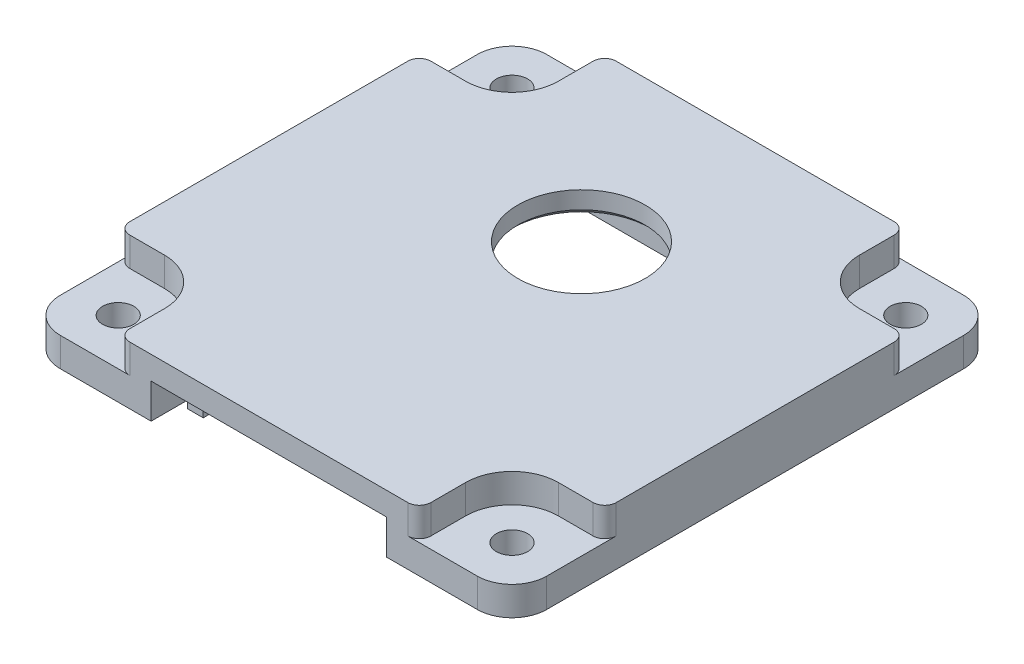
SolidWorks part; units mm, degrees
material "ABS"
ref_plane "Front Plane" through (0, 0, 0) normal (0, 0, 1) x (1, 0, 0)
ref_plane "Top Plane" through (0, 0, 0) normal (0, 1, 0) x (1, 0, 0)
ref_plane "Right Plane" through (0, 0, 0) normal (1, 0, 0) x (0, 0, -1)
sketch "Sketch2" plane through (0, 0, 0) normal (0, 1, 0) x (1, 0, 0)
  line L0 (0, 0) -> (0, 6) construction
  line L1 (-21, 21) -> (21, 21)
  line L2 (-21, 21) -> (-21, -21)
  line L3 (-21, -21) -> (21, -21)
  line L4 (21, 21) -> (21, -21)
  line L5 (-21, 21) -> (21, -21) construction
  line L6 (-21, -21) -> (21, 21) construction
  circle A0 centre (0, 6) radius 5.5
  point P0 (0, 0)
  dimension "D3" = 11
  dimension "D1" = 42
  dimension "D2" = 42
  dimension "D4" = 6
extrude "Boss-Extrude1" add sketch "Sketch2" against normal blind 2
ref_plane "Plane1" through (0, 0, -6) normal (0, 0, 1) x (1, 0, 0)
sketch "Sketch3" plane through (0, 0, -6) normal (0, 0, 1) x (1, 0, 0)
  line L1 (-5.5, 0) -> (-6.25, 0)
  line L2 (-6.25, 0) -> (-6.25, 3)
  line L4 (-6.25, 3) -> (-5.25, 3)
  line L8 (-5.5, 2) -> (-5.5, 0)
  line L9 (0, 0) -> (0, 7.3617) construction
  line L10 (-5.5, 2) -> (-4.5, 2.727)
  line L11 (-4.5, 2.727) -> (-5.25, 3)
  line L13 (0, 1.0892) -> (-5.25, 3) construction
  dimension "D1" = 70
  dimension "D2" = 3
  dimension "D3" = 1
  dimension "D4" = 0.75
  dimension "D5" = 0.75
  dimension "D6" = 2
revolve "Revolve1" [suppressed] add sketch "Sketch3" angle 360 about L9
sketch "Sketch4" plane through (0, -2, 0) normal (0, -1, 0) x (1, 0, 0)
  line L8 (-21, 21) -> (21, 21)
  line L9 (-21, 21) -> (-21, -21)
  line L10 (-21, -21) -> (21, -21)
  line L11 (21, 21) -> (21, -21)
  line L12 (-21, 21) -> (21, -21) construction
  line L13 (-21, -21) -> (21, 21) construction
  line L14 (-17, 11.5228) -> (-17, -11.5228)
  line L15 (-11.5228, -17) -> (11.5228, -17)
  line L16 (17, 11.5228) -> (17, -11.5228)
  line L17 (-11.5228, 17) -> (11.5228, 17)
  arc A12 (-16.5455, -12.0207) -> (-12.0207, -16.5455) centre (-17, -17) cw
  arc A13 (12.0207, -16.5455) -> (16.5455, -12.0207) centre (17, -17) cw
  arc A14 (16.5455, 12.0207) -> (12.0207, 16.5455) centre (17, 17) cw
  arc A15 (-12.0207, 16.5455) -> (-16.5455, 12.0207) centre (-17, 17) cw
  arc A16 (-16.5455, -12.0207) -> (-17, -11.5228) centre (-16.5, -11.5228) cw
  arc A17 (-12.0207, -16.5455) -> (-11.5228, -17) centre (-11.5228, -16.5) ccw
  arc A18 (12.0207, -16.5455) -> (11.5228, -17) centre (11.5228, -16.5) cw
  arc A19 (16.5455, -12.0207) -> (17, -11.5228) centre (16.5, -11.5228) ccw
  arc A20 (16.5455, 12.0207) -> (17, 11.5228) centre (16.5, 11.5228) cw
  arc A21 (12.0207, 16.5455) -> (11.5228, 17) centre (11.5228, 16.5) ccw
  arc A22 (-12.0207, 16.5455) -> (-11.5228, 17) centre (-11.5228, 16.5) cw
  arc A23 (-16.5455, 12.0207) -> (-17, 11.5228) centre (-16.5, 11.5228) ccw
  point P32 (0, 0)
extrude "Boss-Extrude2" add sketch "Sketch4" along normal blind 3
sketch "Sketch6" plane through (0, -2, 0) normal (0, -1, 0) x (1, 0, 0)
  line L8 (-16.5, 11.5228) -> (-16.5, -11.5228)
  line L9 (-11.5228, -16.5) -> (11.5228, -16.5)
  line L10 (16.5, -11.5228) -> (16.5, 11.5228)
  line L11 (11.5228, 16.5) -> (-11.5228, 16.5)
  line L12 (-16.5, 11.5228) -> (-16.5, -11.5228)
  line L13 (-11.5228, -16.5) -> (11.5228, -16.5)
  line L14 (16.5, -11.5228) -> (16.5, 11.5228)
  line L15 (11.5228, 16.5) -> (-11.5228, 16.5)
  line L16 (-17, 11.5228) -> (-17, -11.5228)
  line L17 (-11.5228, -17) -> (11.5228, -17)
  line L18 (17, -11.5228) -> (17, 11.5228)
  line L19 (11.5228, 17) -> (-11.5228, 17)
  line L20 (-17, 11.5228) -> (-17, -11.5228)
  line L21 (-11.5228, -17) -> (11.5228, -17)
  line L22 (17, -11.5228) -> (17, 11.5228)
  line L23 (11.5228, 17) -> (-11.5228, 17)
  arc A24 (-11.5228, -16.5) -> (-16.5, -11.5228) centre (-17, -17) ccw
  arc A25 (16.5, -11.5228) -> (11.5228, -16.5) centre (17, -17) ccw
  arc A26 (11.5228, 16.5) -> (16.5, 11.5228) centre (17, 17) ccw
  arc A27 (-16.5, 11.5228) -> (-11.5228, 16.5) centre (-17, 17) ccw
  arc A28 (-11.5228, -16.5) -> (-16.5, -11.5228) centre (-17, -17) ccw
  arc A29 (16.5, -11.5228) -> (11.5228, -16.5) centre (17, -17) ccw
  arc A30 (11.5228, 16.5) -> (16.5, 11.5228) centre (17, 17) ccw
  arc A31 (-16.5, 11.5228) -> (-11.5228, 16.5) centre (-17, 17) ccw
  arc A32 (-17, -11.5228) -> (-16.5455, -12.0207) centre (-16.5, -11.5228) ccw
  arc A33 (-12.0207, -16.5455) -> (-16.5455, -12.0207) centre (-17, -17) ccw
  arc A34 (-12.0207, -16.5455) -> (-11.5228, -17) centre (-11.5228, -16.5) ccw
  arc A35 (11.5228, -17) -> (12.0207, -16.5455) centre (11.5228, -16.5) ccw
  arc A36 (16.5455, -12.0207) -> (12.0207, -16.5455) centre (17, -17) ccw
  arc A37 (16.5455, -12.0207) -> (17, -11.5228) centre (16.5, -11.5228) ccw
  arc A38 (17, 11.5228) -> (16.5455, 12.0207) centre (16.5, 11.5228) ccw
  arc A39 (12.0207, 16.5455) -> (16.5455, 12.0207) centre (17, 17) ccw
  arc A40 (12.0207, 16.5455) -> (11.5228, 17) centre (11.5228, 16.5) ccw
  arc A41 (-11.5228, 17) -> (-12.0207, 16.5455) centre (-11.5228, 16.5) ccw
  arc A42 (-16.5455, 12.0207) -> (-12.0207, 16.5455) centre (-17, 17) ccw
  arc A43 (-16.5455, 12.0207) -> (-17, 11.5228) centre (-16.5, 11.5228) ccw
  arc A44 (-17, -11.5228) -> (-16.5455, -12.0207) centre (-16.5, -11.5228) ccw
  arc A45 (-12.0207, -16.5455) -> (-16.5455, -12.0207) centre (-17, -17) ccw
  arc A46 (-12.0207, -16.5455) -> (-11.5228, -17) centre (-11.5228, -16.5) ccw
  arc A47 (11.5228, -17) -> (12.0207, -16.5455) centre (11.5228, -16.5) ccw
  arc A48 (16.5455, -12.0207) -> (12.0207, -16.5455) centre (17, -17) ccw
  arc A49 (16.5455, -12.0207) -> (17, -11.5228) centre (16.5, -11.5228) ccw
  arc A50 (17, 11.5228) -> (16.5455, 12.0207) centre (16.5, 11.5228) ccw
  arc A51 (12.0207, 16.5455) -> (16.5455, 12.0207) centre (17, 17) ccw
  arc A52 (12.0207, 16.5455) -> (11.5228, 17) centre (11.5228, 16.5) ccw
  arc A53 (-11.5228, 17) -> (-12.0207, 16.5455) centre (-11.5228, 16.5) ccw
  arc A54 (-16.5455, 12.0207) -> (-12.0207, 16.5455) centre (-17, 17) ccw
  arc A55 (-16.5455, 12.0207) -> (-17, 11.5228) centre (-16.5, 11.5228) ccw
  dimension "D1" = 0.5
  dimension "D2" = 0
extrude "Boss-Extrude3" add sketch "Sketch6" along normal up to surface (3 mm away) up to face at (0, -5, 0)
sketch "Sketch7" plane through (0, -2, 0) normal (0, -1, 0) x (1, 0, 0)
  line L8 (10.6754, 15.5) -> (-10.6754, 15.5)
  line L9 (-15.5, 10.6754) -> (-15.5, -10.6754)
  line L10 (-10.6754, -15.5) -> (10.6754, -15.5)
  line L11 (15.5, -10.6754) -> (15.5, 10.6754)
  line L12 (10.6754, 15.5) -> (-10.6754, 15.5)
  line L13 (-15.5, 10.6754) -> (-15.5, -10.6754)
  line L14 (-10.6754, -15.5) -> (10.6754, -15.5)
  line L15 (15.5, -10.6754) -> (15.5, 10.6754)
  line L16 (11.5228, 16.5) -> (-11.5228, 16.5)
  line L17 (-16.5, 11.5228) -> (-16.5, -11.5228)
  line L18 (-11.5228, -16.5) -> (11.5228, -16.5)
  line L19 (16.5, -11.5228) -> (16.5, 11.5228)
  line L20 (11.5228, 16.5) -> (-11.5228, 16.5)
  line L21 (-16.5, 11.5228) -> (-16.5, -11.5228)
  line L22 (-11.5228, -16.5) -> (11.5228, -16.5)
  line L23 (16.5, -11.5228) -> (16.5, 11.5228)
  arc A8 (10.6754, 15.5) -> (15.5, 10.6754) centre (17, 17) ccw
  arc A9 (-15.5, 10.6754) -> (-10.6754, 15.5) centre (-17, 17) ccw
  arc A10 (-10.6754, -15.5) -> (-15.5, -10.6754) centre (-17, -17) ccw
  arc A11 (15.5, -10.6754) -> (10.6754, -15.5) centre (17, -17) ccw
  arc A12 (10.6754, 15.5) -> (15.5, 10.6754) centre (17, 17) ccw
  arc A13 (-15.5, 10.6754) -> (-10.6754, 15.5) centre (-17, 17) ccw
  arc A14 (-10.6754, -15.5) -> (-15.5, -10.6754) centre (-17, -17) ccw
  arc A15 (15.5, -10.6754) -> (10.6754, -15.5) centre (17, -17) ccw
  arc A16 (11.5228, 16.5) -> (16.5, 11.5228) centre (17, 17) ccw
  arc A17 (-16.5, 11.5228) -> (-11.5228, 16.5) centre (-17, 17) ccw
  arc A18 (-11.5228, -16.5) -> (-16.5, -11.5228) centre (-17, -17) ccw
  arc A19 (16.5, -11.5228) -> (11.5228, -16.5) centre (17, -17) ccw
  arc A20 (11.5228, 16.5) -> (16.5, 11.5228) centre (17, 17) ccw
  arc A21 (-16.5, 11.5228) -> (-11.5228, 16.5) centre (-17, 17) ccw
  arc A22 (-11.5228, -16.5) -> (-16.5, -11.5228) centre (-17, -17) ccw
  arc A23 (16.5, -11.5228) -> (11.5228, -16.5) centre (17, -17) ccw
  dimension "D1" = 1
  dimension "D2" = 0
extrude "Boss-Extrude5" add sketch "Sketch7" along normal blind 5
sketch "Sketch9" plane through (0, 0, 0) normal (0, 1, 0) x (1, 0, 0)
  circle A0 centre (-17, 17) radius 1.35
  circle A1 centre (17, 17) radius 1.35
  circle A2 centre (-17, -17) radius 1.35
  circle A3 centre (17, -17) radius 1.35
  dimension "D1" = 2.7
sketch "Sketch8" plane through (0, 0, 0) normal (0, 1, 0) x (1, 0, 0)
  line L0 (-17, 13) -> (-21, 13)
  line L1 (-21, -21) -> (-21, 21) construction
  line L2 (-21, 13) -> (-21, 21)
  line L3 (-13, 17) -> (-13, 21)
  line L4 (-21, 21) -> (21, 21) construction
  line L5 (-13, 21) -> (-21, 21)
  line L6 (13, 17) -> (13, 21)
  line L7 (13, 21) -> (21, 21)
  line L8 (21, 21) -> (21, 13)
  line L9 (17, 13) -> (21, 13)
  line L10 (21, -21) -> (21, 21) construction
  line L11 (-21, -17) -> (-21, -21)
  line L12 (-21, -21) -> (-17, -21)
  line L13 (-21, -21) -> (21, -21) construction
  line L14 (-13, -17) -> (-13, -21)
  line L15 (-13, -21) -> (-17, -21)
  line L16 (-17, -13) -> (-21, -13)
  line L17 (-21, -13) -> (-21, -17)
  line L18 (17, -13) -> (21, -13)
  line L19 (21, -13) -> (21, -21)
  line L20 (21, -21) -> (17, -21)
  line L21 (13, -17) -> (13, -21)
  line L22 (13, -21) -> (17, -21)
  arc A0 (-17, 13) -> (-13, 17) centre (-17, 17) ccw
  arc A2 (13, 17) -> (17, 13) centre (17, 17) ccw
  arc A3 (17, -13) -> (13, -17) centre (17, -17) ccw
  arc A4 (-13, -17) -> (-17, -13) centre (-17, -17) ccw
extrude "Cut-Extrude1" cut sketch "Sketch8" against normal blind 2.5
extrude "Cut-Extrude2" cut sketch "Sketch9" against normal through all
fillet "Fillet1" radius 3 4 edges at (21, -3.75, 21) (-21, -3.75, 21) (21, -3.75, -21) (-21, -3.75, -21)
fillet "Fillet2" radius 1 8 edges at (-21, -1.25, -13) (-13, -1.25, -21) (13, -1.25, -21) (21, -1.25, -13) (21, -1.25, 13) (13, -1.25, 21) (-13, -1.25, 21) (-21, -1.25, 13)
chamfer "Chamfer1" distance 0.5 angle 45 1 edges at (0, -2, -0.5)
chamfer "Chamfer2" [suppressed] distance 0.5 angle 45
sketch "Sketch10" plane through (0, 0, 21) normal (0, 0, 1) x (1, 0, 0)
  line L0 (11.5228, -7) -> (-11.5228, -7) construction
  line L1 (-10.16, -2) -> (10.16, -2)
  line L2 (-10.16, -2) -> (-10.16, -7)
  line L3 (-10.16, -7) -> (10.16, -7)
  line L4 (10.16, -2) -> (10.16, -7)
  line L5 (-10.16, -2) -> (10.16, -7) construction
  line L6 (-10.16, -7) -> (10.16, -2) construction
  point P0 (0, -4.5)
  point P5 (0, -2)
  point P9 (0, -7)
  point P10 (0, -7)
  dimension "D1" = 20.32
  dimension "D2" = 5
extrude "Cut-Extrude3" cut sketch "Sketch10" against normal up to surface (5.5 mm away) up to face at (0, -4.5, 15.5)
